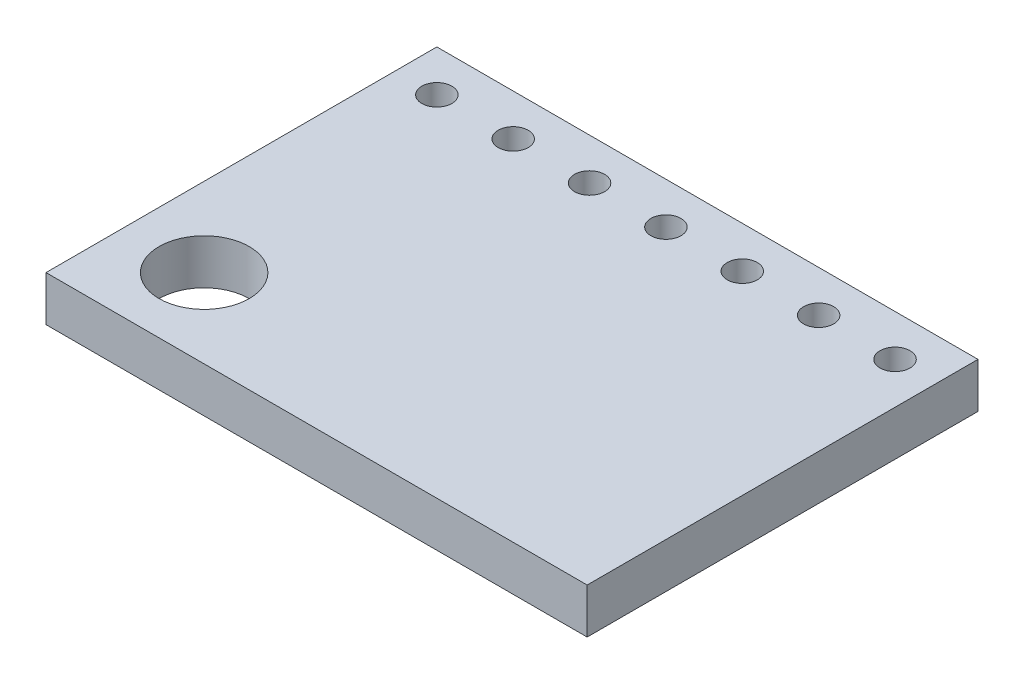
SolidWorks part; units mm, degrees
material "Brass"
ref_plane "Front Plane" through (0, 0, 0) normal (0, 0, 1) x (1, 0, 0)
ref_plane "Top Plane" through (0, 0, 0) normal (0, 1, 0) x (1, 0, 0)
ref_plane "Right Plane" through (0, 0, 0) normal (1, 0, 0) x (0, 0, -1)
sketch "Sketch1" plane through (0, 0, 0) normal (0, 1, 0) x (1, 0, 0)
  line L0 (1.38, -1.38) -> (3.92, -1.38) construction
  line L1 (0, 0) -> (18, 0)
  line L2 (0, 0) -> (0, -13)
  line L3 (0, -13) -> (18, -13)
  line L4 (18, 0) -> (18, -13)
  circle A0 centre (1.38, -1.38) radius 0.5
  circle A1 centre (3.92, -1.38) radius 0.5
  circle A2 centre (6.46, -1.38) radius 0.5
  circle A3 centre (9, -1.38) radius 0.5
  circle A4 centre (11.54, -1.38) radius 0.5
  circle A5 centre (14.08, -1.38) radius 0.5
  circle A6 centre (16.62, -1.38) radius 0.5
  circle A7 centre (2.63, -10.37) radius 1.5
  dimension "D3" = 7
  dimension "D5" = 1
  dimension "D8" = 3
  dimension "D1" = 18
  dimension "D2" = 13
  dimension "D4" = 2.54
  dimension "D6" = 1.38
  dimension "D7" = 1.38
  dimension "D9" = 2.63
  dimension "D10" = 2.63
extrude "Boss-Extrude1" add sketch "Sketch1" against normal blind 1.5
